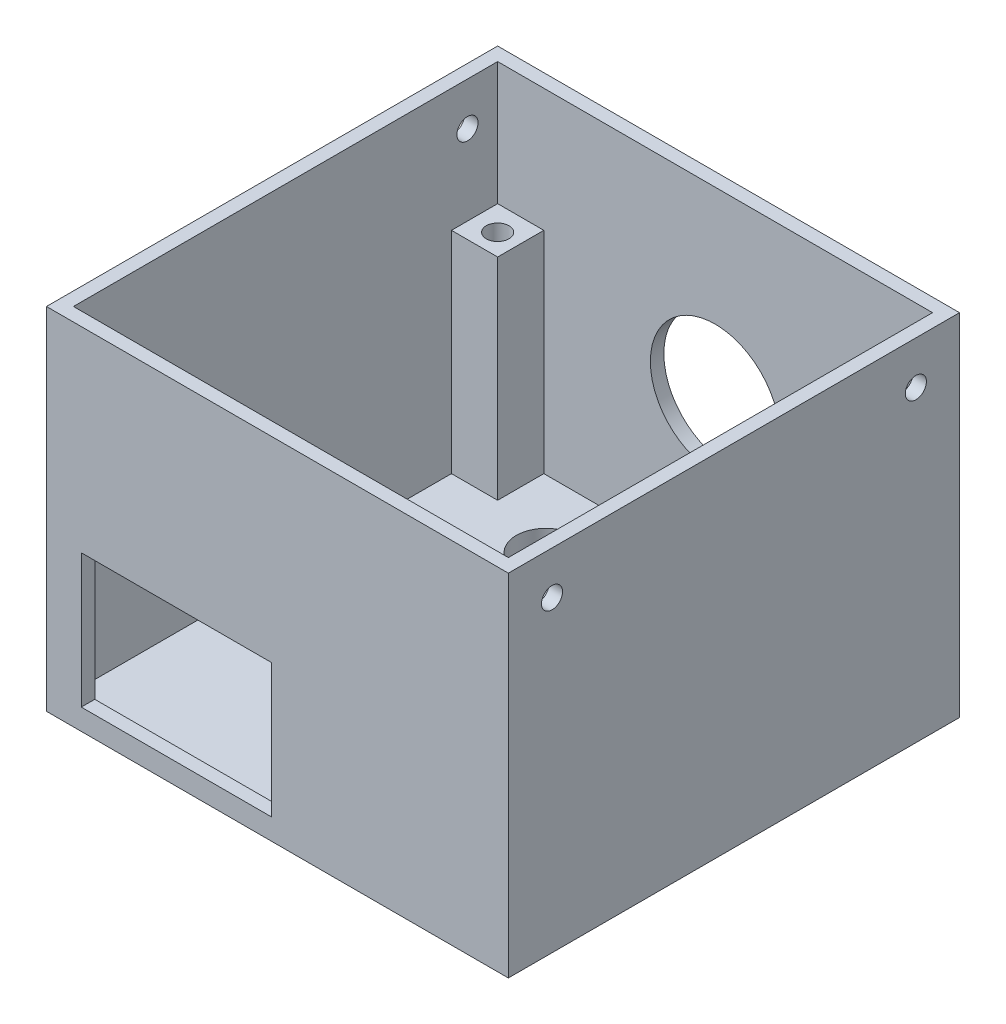
SolidWorks part; units mm, degrees
ref_plane "Front Plane" through (0, 0, 0) normal (0, 0, 1) x (1, 0, 0)
ref_plane "Top Plane" through (0, 0, 0) normal (0, 1, 0) x (1, 0, 0)
ref_plane "Right Plane" through (0, 0, 0) normal (1, 0, 0) x (0, 0, -1)
sketch "Sketch1" plane through (0, 0, 0) normal (0, 1, 0) x (1, 0, 0)
  line L1 (27.4, -26.765) -> (-27.4, -26.765)
  line L2 (27.4, -26.765) -> (27.4, 26.765)
  line L3 (27.4, 26.765) -> (-27.4, 26.765)
  line L4 (-27.4, -26.765) -> (-27.4, 26.765)
  line L5 (27.4, -26.765) -> (-27.4, 26.765) construction
  line L6 (27.4, 26.765) -> (-27.4, -26.765) construction
  point P0 (0, 0)
  dimension "D1" = 54.8
  dimension "D2" = 53.53
extrude "Boss-Extrude1" add sketch "Sketch1" along normal blind 41.6
sketch "Sketch2" plane through (0, 41.6, 0) normal (0, 1, 0) x (1, 0, 0)
  line L0 (-27.4, 26.765) -> (-27.4, -26.765) construction
  line L1 (25.8, -25.165) -> (-25.8, -25.165)
  line L2 (25.8, -25.165) -> (25.8, 25.165)
  line L3 (25.8, 25.165) -> (-25.8, 25.165)
  line L4 (-25.8, -25.165) -> (-25.8, 25.165)
  line L5 (25.8, -25.165) -> (-25.8, 25.165) construction
  line L6 (25.8, 25.165) -> (-25.8, -25.165) construction
  line L7 (27.4, 26.765) -> (-27.4, 26.765) construction
  point P0 (0, 0)
  dimension "D1" = 1.6
  dimension "D2" = 1.6
extrude "Cut-Extrude1" cut sketch "Sketch2" against normal blind 39.6
sketch "Sketch3" plane through (0, 2, 0) normal (0, 1, 0) x (1, 0, 0)
  line L1 (-25.8, 25.165) -> (-20.32, 25.165)
  line L2 (-25.8, 25.165) -> (-25.8, 19.685)
  line L3 (-25.8, 19.685) -> (-20.32, 19.685)
  line L4 (-20.32, 25.165) -> (-20.32, 19.685)
  line L5 (25.8, 25.165) -> (20.32, 25.165)
  line L6 (25.8, 25.165) -> (25.8, 19.685)
  line L7 (25.8, 19.685) -> (20.32, 19.685)
  line L8 (20.32, 25.165) -> (20.32, 19.685)
  line L9 (25.8, -25.165) -> (20.32, -25.165)
  line L10 (25.8, -25.165) -> (25.8, -19.685)
  line L11 (25.8, -19.685) -> (20.32, -19.685)
  line L12 (20.32, -25.165) -> (20.32, -19.685)
  dimension "D1" = 5.48
  dimension "D2" = 5.48
  dimension "D3" = 5.48
  dimension "D4" = 5.48
  dimension "D5" = 5.48
  dimension "D6" = 5.48
extrude "Boss-Extrude2" add sketch "Sketch3" along normal blind 25
sketch "Sketch4" plane through (0, 27, 0) normal (0, 1, 0) x (1, 0, 0)
  line L0 (-20.32, 19.685) -> (-20.32, 25.165) construction
  line L3 (-25.8, 19.685) -> (-20.32, 19.685) construction
  line L4 (20.32, 19.685) -> (25.8, 19.685) construction
  line L5 (20.32, 25.165) -> (20.32, 19.685) construction
  line L6 (25.8, -19.685) -> (20.32, -19.685) construction
  line L7 (20.32, -19.685) -> (20.32, -25.165) construction
  circle A0 centre (-22.86, 22.225) radius 1.35
  circle A1 centre (22.86, 22.225) radius 1.35
  circle A2 centre (22.86, -22.2171) radius 1.35
  point P12 (23.06, -19.685)
  dimension "D1" = 2.54
  dimension "D3" = 2.54
  dimension "D5" = 2.54
  dimension "D2" = 2.54
  dimension "D4" = 2.54
  dimension "D6" = 2.54
extrude "Cut-Extrude2" cut sketch "Sketch4" against normal blind 10
sketch "Sketch5" plane through (0, 0, 0) normal (0, -1, 0) x (-1, 0, 0)
  circle A0 centre (-12.7629, 17.1869) radius 3.5
  circle A1 centre (12.1084, 17.1869) radius 3.5
extrude "Cut-Extrude3" cut sketch "Sketch5" against normal up to next
sketch "Sketch6" plane through (0, 0, 0) normal (0, -1, 0) x (-1, 0, 0)
  circle A0 centre (-16.9081, 1.5272) radius 3.1
  circle A1 centre (-8.7267, 1.5272) radius 3.1
extrude "Cut-Extrude4" cut sketch "Sketch6" against normal up to next
sketch "Sketch7" plane through (0, 0, 0) normal (0, -1, 0) x (-1, 0, 0)
  circle A0 centre (-12.6538, -10.0358) radius 3.6
extrude "Cut-Extrude5" cut sketch "Sketch7" against normal up to next
sketch "Sketch8" plane through (27.4, 0, 0) normal (1, 0, 0) x (0, 0, -1)
  line L0 (-26.765, 41.6) -> (26.765, 41.6) construction
  line L1 (-26.765, 41.6) -> (-26.765, 0) construction
  circle A0 centre (-21.585, 36.49) radius 1.25
  dimension "D1" = 5.11
  dimension "D2" = 5.18
extrude "Cut-Extrude6" cut sketch "Sketch8" against normal up to next
sketch "Sketch10" plane through (-27.4, 0, 0) normal (-1, 0, 0) x (0, 0, 1)
  line L0 (-26.765, 41.6) -> (26.765, 41.6) construction
  line L1 (-26.765, 41.6) -> (-26.765, 0) construction
  circle A0 centre (-21.585, 36.49) radius 1.25
  dimension "D1" = 5.11
  dimension "D2" = 5.18
extrude "Cut-Extrude7" cut sketch "Sketch10" against normal up to next
sketch "Sketch12" plane through (0, 0, -26.765) normal (0, 0, -1) x (-1, 0, 0)
  circle A0 centre (0, 19.8508) radius 7.6805
extrude "Cut-Extrude8" cut sketch "Sketch12" against normal up to next
sketch "Sketch13" plane through (0, 0, 26.765) normal (0, 0, 1) x (1, 0, 0)
  line L0 (-27.4, 0) -> (27.4, 0) construction
  line L1 (-0.6897, 2.5) -> (-23.2715, 2.5)
  line L2 (-0.6897, 2.5) -> (-0.6897, 18.3624)
  line L3 (-0.6897, 18.3624) -> (-23.2715, 18.3624)
  line L4 (-23.2715, 2.5) -> (-23.2715, 18.3624)
  line L5 (-0.6897, 2.5) -> (-23.2715, 18.3624) construction
  line L6 (-0.6897, 18.3624) -> (-23.2715, 2.5) construction
  point P0 (-11.9806, 10.4312)
  dimension "D1" = 2.5
extrude "Cut-Extrude9" cut sketch "Sketch13" against normal up to next
sketch "Sketch14" plane through (27.4, 0, 0) normal (1, 0, 0) x (0, 0, -1)
  line L0 (-26.765, 41.6) -> (26.765, 41.6) construction
  line L2 (26.765, 41.6) -> (26.765, 0) construction
  circle A0 centre (21.585, 36.49) radius 1.25
  point P6 (26.765, 36.4016)
  dimension "D1" = 5.11
  dimension "D2" = 5.18
extrude "Cut-Extrude10" cut sketch "Sketch14" against normal up to next
